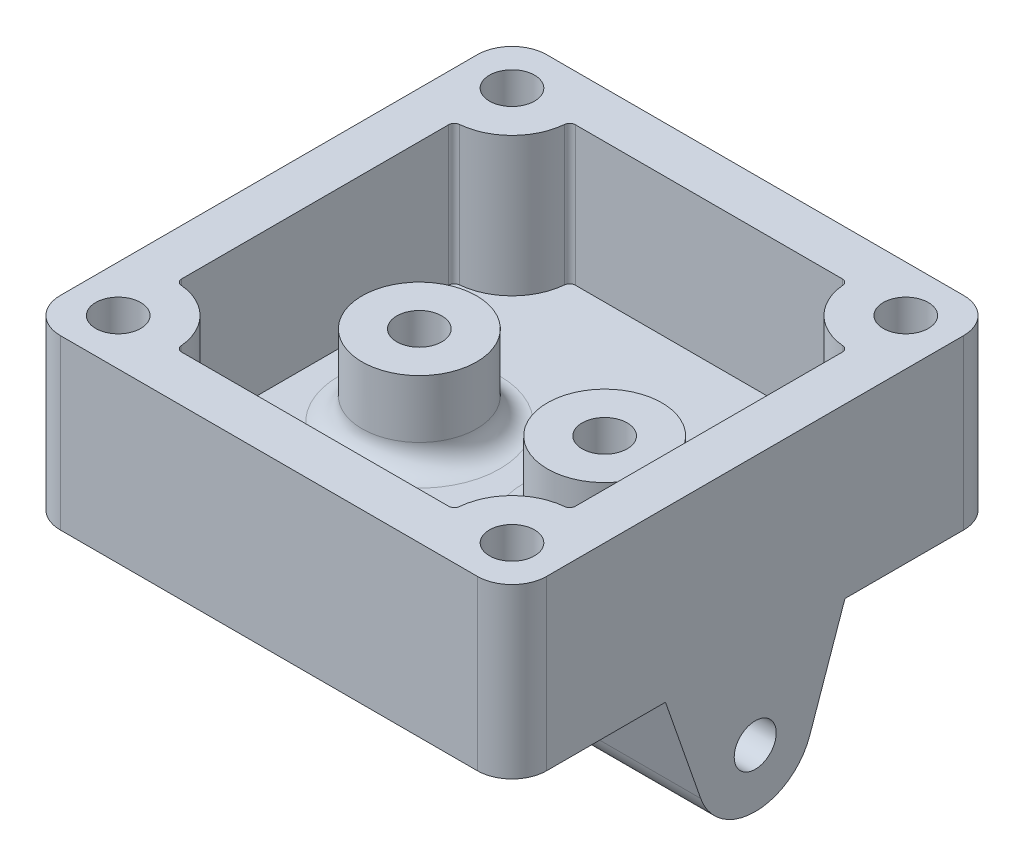
SolidWorks part; units mm, degrees
ref_plane "Front Plane" through (0, 0, 0) normal (0, 0, 1) x (1, 0, 0)
ref_plane "Top Plane" through (0, 0, 0) normal (0, 1, 0) x (1, 0, 0)
ref_plane "Right Plane" through (0, 0, 0) normal (1, 0, 0) x (0, 0, -1)
sketch "Sketch1" plane through (0, 0, 0) normal (0, 1, 0) x (1, 0, 0)
  line L1 (-21, 21) -> (21, 21)
  line L2 (-21, 21) -> (-21, -21)
  line L3 (-21, -21) -> (21, -21)
  line L4 (21, 21) -> (21, -21)
  line L5 (-21, 21) -> (21, -21) construction
  line L6 (-21, -21) -> (21, 21) construction
  point P0 (0, 0)
  dimension "D1" = 42
  dimension "D2" = 42
extrude "Boss-Extrude1" add sketch "Sketch1" along normal blind 2.54
sketch "Sketch2" plane through (0, 2.54, 0) normal (0, 1, 0) x (1, 0, 0)
  line L26 (-21, 21) -> (21, 21)
  line L44 (-21, 21) -> (-21, -21)
  line L45 (-21, -21) -> (21, -21)
  line L49 (21, 21) -> (21, -21)
  line L50 (-21, 21) -> (21, -21) construction
  line L51 (-21, -21) -> (21, 21) construction
  line L55 (-17, 11.5228) -> (-17, -11.5228)
  line L56 (-11.5228, -17) -> (11.5228, -17)
  line L57 (17, 11.5228) -> (17, -11.5228)
  line L58 (-11.5228, 17) -> (11.5228, 17)
  line L63 (-17, 17) -> (-17, -17) construction
  line L64 (-17, -17) -> (17, -17) construction
  line L65 (17, 17) -> (17, -17) construction
  line L66 (-17, 17) -> (17, 17) construction
  line L68 (-13.4645, 13.4645) -> (13.4645, 13.4645) construction
  line L69 (-13.4645, 13.4645) -> (-13.4645, -13.4645) construction
  line L70 (-13.4645, -13.4645) -> (13.4645, -13.4645) construction
  line L71 (13.4645, 13.4645) -> (13.4645, -13.4645) construction
  line L72 (-13.4645, 13.4645) -> (13.4645, -13.4645) construction
  line L73 (-13.4645, -13.4645) -> (13.4645, 13.4645) construction
  arc A0 (-16.5455, -12.0207) -> (-12.0207, -16.5455) centre (-17, -17) cw
  arc A2 (12.0207, -16.5455) -> (16.5455, -12.0207) centre (17, -17) cw
  arc A4 (16.5455, 12.0207) -> (12.0207, 16.5455) centre (17, 17) cw
  arc A6 (-12.0207, 16.5455) -> (-16.5455, 12.0207) centre (-17, 17) cw
  arc A8 (-16.5455, -12.0207) -> (-17, -11.5228) centre (-16.5, -11.5228) cw
  arc A9 (-12.0207, -16.5455) -> (-11.5228, -17) centre (-11.5228, -16.5) ccw
  arc A10 (12.0207, -16.5455) -> (11.5228, -17) centre (11.5228, -16.5) cw
  arc A11 (16.5455, -12.0207) -> (17, -11.5228) centre (16.5, -11.5228) ccw
  arc A12 (16.5455, 12.0207) -> (17, 11.5228) centre (16.5, 11.5228) cw
  arc A13 (12.0207, 16.5455) -> (11.5228, 17) centre (11.5228, 16.5) ccw
  arc A14 (-12.0207, 16.5455) -> (-11.5228, 17) centre (-11.5228, 16.5) cw
  arc A15 (-16.5455, 12.0207) -> (-17, 11.5228) centre (-16.5, 11.5228) ccw
  point P0 (0, 0)
  point P44 (0, 0)
  dimension "D2" = 5
  dimension "D3" = 0.5
  dimension "D1" = 4
  dimension "D4" = 26.9289
extrude "Boss-Extrude2" add sketch "Sketch2" along normal blind 12
sketch "Sketch4" plane through (-21, 0, 0) normal (-1, 0, 0) x (0, 0, 1)
  line L0 (7.7485, 0) -> (4.709, -8.7193)
  line L1 (-21, 0) -> (21, 0) construction
  line L2 (-4.709, -8.7193) -> (-7.7485, 0)
  line L3 (7.7485, 0) -> (-7.7485, 0)
  arc A0 (4.709, -8.7193) -> (-4.709, -8.7193) centre (0, -7.0778) cw
  circle A1 centre (0, -7.0778) radius 1.8138
extrude "Boss-Extrude4" add sketch "Sketch4" against normal up to surface (42 mm away) up to face at (21, 7.27, 0)
mirror "Mirror1" [suppressed] about plane through (0, 0, 0) normal (1, 0, 0)
sketch "Sketch9" plane through (0, 2.54, 0) normal (0, 1, 0) x (1, 0, 0)
  line L0 (0, -7.997) -> (0, 7.997) construction
  line L1 (0, 0) -> (-8, 0) construction
  circle A0 centre (8, 0) radius 1.945
  circle A1 centre (8, 0) radius 4.945
  circle A2 centre (-8, 0) radius 4.945
  circle A3 centre (-8, 0) radius 1.945
  dimension "D1" = 3.89
  dimension "D2" = 3
  dimension "D3" = 8
extrude "Boss-Extrude5" add sketch "Sketch9" along normal blind 7
sketch "Sketch10" plane through (0, 14.54, 0) normal (0, 1, 0) x (1, 0, 0)
  circle A0 centre (-17, 17) radius 1.945
  circle A1 centre (17, 17) radius 1.945
  circle A2 centre (-17, -17) radius 1.945
  circle A3 centre (17, -17) radius 1.945
  dimension "D1" = 3.89
extrude "Cut-Extrude1" cut sketch "Sketch10" against normal blind 8
fillet "Fillet1" radius 3 4 edges at (21, 7.27, 21) (-21, 7.27, 21) (-21, 7.27, -21) (21, 7.27, -21)
fillet "Fillet2" [suppressed] radius 2
fillet "Fillet3" radius 2 2 edges at (-8, 2.54, -4.945) (8, 2.54, 4.945)
